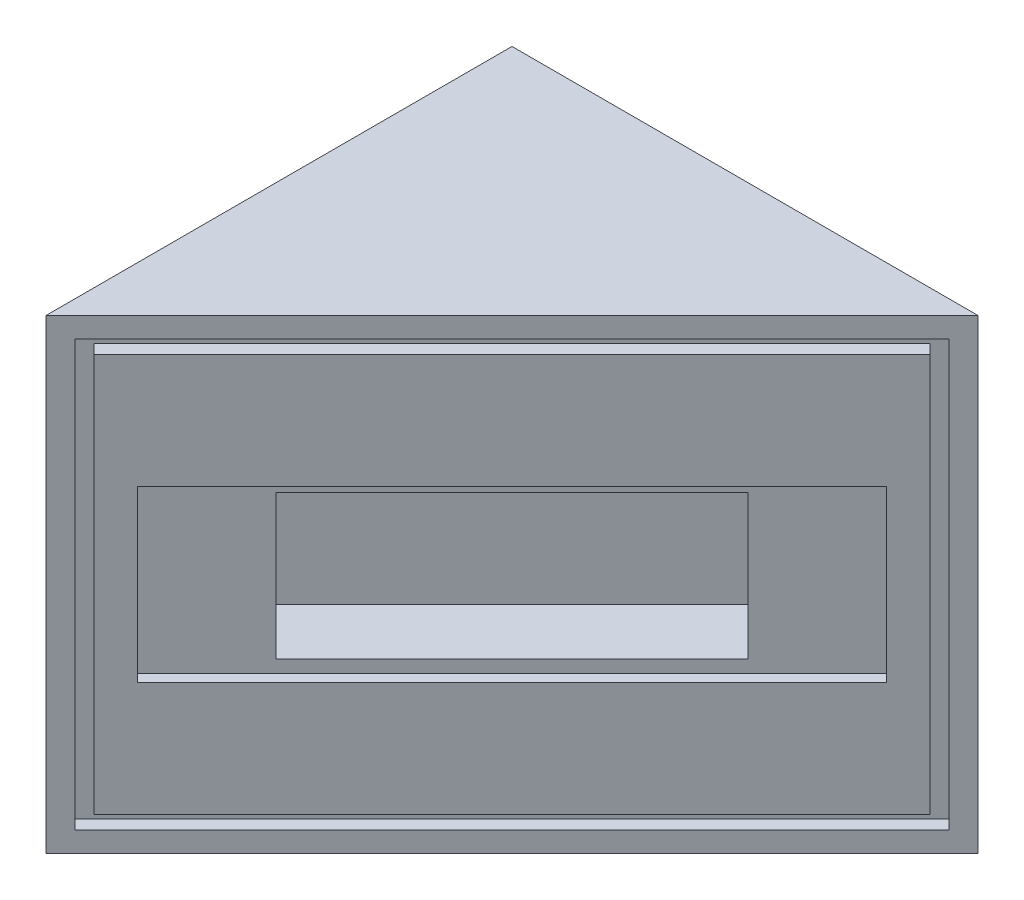
SolidWorks part; units mm, degrees
ref_plane "Front Plane" through (0, 0, 0) normal (0, 0, 1) x (1, 0, 0)
ref_plane "Top Plane" through (0, 0, 0) normal (0, 1, 0) x (1, 0, 0)
ref_plane "Right Plane" through (0, 0, 0) normal (1, 0, 0) x (0, 0, -1)
sketch "Sketch1" plane through (0, 0, 0) normal (0, 1, 0) x (1, 0, 0)
  line L1 (0, 0) -> (69.85, 0)
  line L2 (0, 0) -> (0, 69.85)
  line L3 (0, 69.85) -> (69.85, 69.85)
  line L4 (69.85, 0) -> (69.85, 69.85)
  dimension "D1" = 69.85
  dimension "D2" = 69.85
extrude "Boss-Extrude1" add sketch "Sketch1" along normal blind 69.85
ref_plane "Plane1" through (0, 0, 0) normal (0.7071, 0, 0.7071) x (0.7071, 0, -0.7071)
sketch "Sketch2" plane through (0, 0, 0) normal (0.7071, 0, 0.7071) x (0.7071, 0, -0.7071)
  line L0 (98.7828, 69.85) -> (98.7828, 0) construction
  line L1 (98.7828, 0) -> (49.3914, 0) construction
  line L2 (49.3914, 0) -> (0, 0) construction
  line L3 (0, 69.85) -> (0, 0) construction
  line L4 (49.3914, 69.85) -> (0, 69.85) construction
  line L5 (98.7828, 69.85) -> (49.3914, 69.85) construction
  line L6 (98.7828, 69.85) -> (98.7828, 0)
  line L7 (98.7828, 0) -> (49.3914, 0)
  line L8 (49.3914, 0) -> (0, 0)
  line L9 (0, 69.85) -> (0, 0)
  line L10 (49.3914, 69.85) -> (0, 69.85)
  line L11 (98.7828, 69.85) -> (49.3914, 69.85)
extrude "Cut-Extrude2" cut sketch "Sketch2" along normal blind 100
surface "Surface-Knit1"
sketch "Sketch3" plane through (0, 0, 0) normal (0.7071, 0, 0.7071) x (0.7071, 0, -0.7071)
  line L0 (3.048, 66.802) -> (98.7828, 0) construction
  line L1 (49.3914, 3.048) -> (49.3914, 66.802) construction
  line L2 (3.048, 34.925) -> (95.7348, 34.925) construction
  line L4 (0, 69.85) -> (0, 0) construction
  line L5 (0, 0) -> (98.7828, 0) construction
  line L6 (98.7828, 69.85) -> (0, 69.85) construction
  line L7 (98.7828, 69.85) -> (98.7828, 0) construction
  line L24 (93.7028, 64.77) -> (5.08, 64.77)
  line L25 (5.08, 64.77) -> (5.08, 5.08)
  line L26 (5.08, 5.08) -> (93.7028, 5.08)
  line L27 (93.7028, 5.08) -> (93.7028, 64.77)
  line L32 (95.7348, 66.802) -> (3.048, 66.802)
  line L33 (3.048, 66.802) -> (3.048, 3.048)
  line L34 (3.048, 3.048) -> (95.7348, 3.048)
  line L35 (95.7348, 3.048) -> (95.7348, 66.802)
  dimension "D1" = 3.048
  dimension "D2" = 3.048
  dimension "D3" = 3.048
  dimension "D4" = 3.048
  dimension "D5" = 2.032
  dimension "D6" = 2.032
  dimension "D7" = 2.032
  dimension "D8" = 2.032
extrude "Cut-Extrude4" cut sketch "Sketch3" against normal blind 2.032
sketch "Sketch4" plane through (0, 0, 0) normal (0.7071, 0, 0.7071) x (0.7071, 0, -0.7071)
  line L0 (5.08, 64.77) -> (93.7028, 5.08) construction
  line L1 (93.7028, 64.77) -> (5.08, 5.08) construction
  line L2 (9.7039, 47.625) -> (89.0789, 22.225) construction
  line L3 (89.0789, 47.625) -> (9.7039, 22.225) construction
  line L12 (9.7039, 22.225) -> (89.0789, 22.225)
  line L13 (89.0789, 22.225) -> (89.0789, 47.625)
  line L14 (89.0789, 47.625) -> (9.7039, 47.625)
  line L15 (9.7039, 47.625) -> (9.7039, 22.225)
  point P4 (49.3914, 34.925)
  point P5 (49.3914, 34.925)
  dimension "D1" = 79.375
  dimension "D2" = 25.4
extrude "Cut-Extrude5" cut sketch "Sketch4" against normal blind 1.6
sketch "Sketch5" plane through (-1.1314, 0, -1.1314) normal (0.7071, 0, 0.7071) x (0.7071, 0, -0.7071)
  line L0 (0, 69.85) -> (98.7828, 0) construction
  line L1 (0, 0) -> (98.7828, 0) construction
  line L2 (98.7828, 69.85) -> (98.7828, 0) construction
  line L3 (98.7828, 69.85) -> (0, 0) construction
  line L5 (24.3914, 45.72) -> (74.3914, 45.72)
  line L6 (24.3914, 45.72) -> (24.3914, 24.13)
  line L7 (24.3914, 24.13) -> (74.3914, 24.13)
  line L8 (74.3914, 45.72) -> (74.3914, 24.13)
  line L9 (24.3914, 45.72) -> (74.3914, 24.13) construction
  line L10 (24.3914, 24.13) -> (74.3914, 45.72) construction
  point P11 (49.3914, 34.925)
  dimension "D1" = 50
  dimension "D2" = 21.59
extrude "Cut-Extrude6" cut sketch "Sketch5" against normal blind 10
